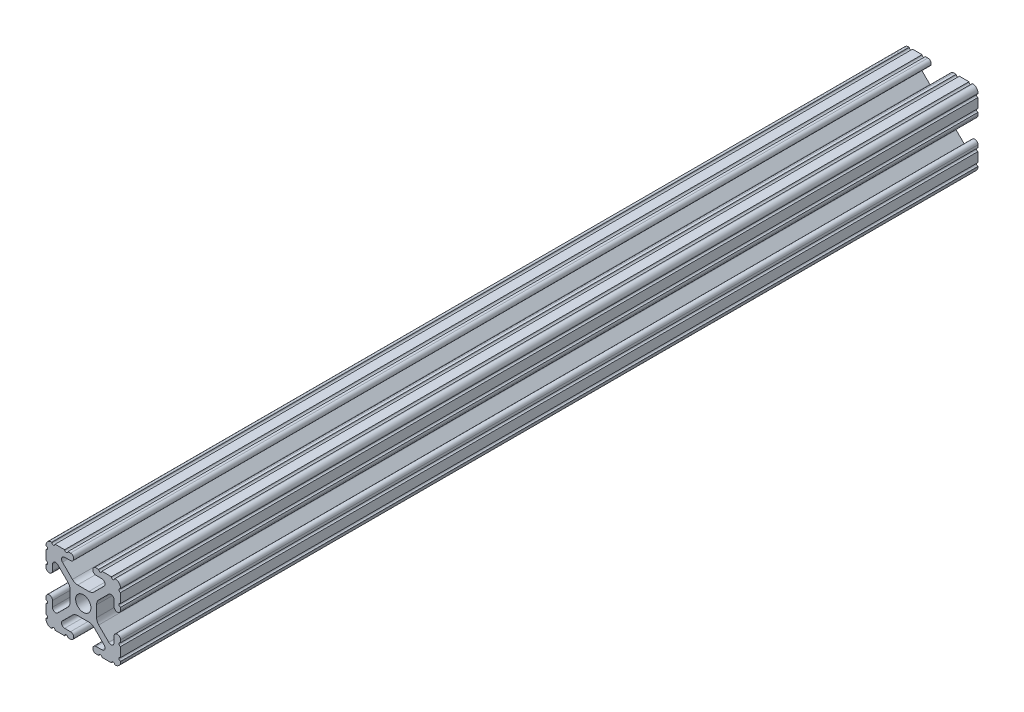
SolidWorks part; units mm, degrees
ref_plane "Front Plane" through (0, 0, 0) normal (0, 0, 1) x (1, 0, 0)
ref_plane "Top Plane" through (0, 0, 0) normal (0, 1, 0) x (1, 0, 0)
ref_plane "Right Plane" through (0, 0, 0) normal (1, 0, 0) x (0, 0, -1)
sketch "Sketch1" plane through (0, 0, 0) normal (0, 0, 1) x (1, 0, 0)
  line L0 (0, -12.7) -> (0, 12.7) construction
  line L1 (12.7, 0) -> (-12.7, 0) construction
  line L2 (3.2512, 12.7) -> (-3.2512, 12.7) construction
  line L3 (0, -4.5212) -> (0, 4.5212) construction
  line L4 (-3.2512, 12.7) -> (-3.2512, 10.4902) construction
  line L5 (12.7, -7.4168) -> (12.7, 7.4168) construction
  line L6 (0, -2.6035) -> (0, 2.6035) construction
  point P4 (0, 0)
  point P8 (0, 0)
  point P11 (0, 12.7)
  point P14 (0, 0)
  point P18 (12.7, 0)
  point P21 (0, 0)
sketch "Sketch2" plane through (0, 0, 0) normal (1, 0, 0) x (0, 0, -1)
  line L0 (-146.05, 0) -> (146.05, 0) construction
  point P4 (0, 0)
  dimension "Length" = 292.1
sketch "Sketch3" plane through (0, 0, 0) normal (0, 0, 1) x (1, 0, 0)
  line L1 (12.7, -12.7) -> (-12.7, -12.7)
  line L2 (12.7, -12.7) -> (12.7, 12.7)
  line L3 (12.7, 12.7) -> (-12.7, 12.7)
  line L4 (-12.7, -12.7) -> (-12.7, 12.7)
  line L5 (12.7, -12.7) -> (-12.7, 12.7) construction
  line L6 (12.7, 12.7) -> (-12.7, -12.7) construction
  point P0 (0, 0)
extrude "Boss-Extrude1" add sketch "Sketch3" along normal up to vertex (146.05 mm away) and the other way up to vertex (146.05 mm away) up to point (0, 0, 146.05) other way up to point (0, 0, -146.05)
sketch "Sketch4" plane through (0, 0, 146.05) normal (0, 0, 1) x (1, 0, 0)
  line L0 (-3.2512, 12.7) -> (-3.2512, 10.4902)
  line L1 (-3.2512, 10.4902) -> (-8.9276, 10.4902)
  line L2 (-8.9276, 10.4902) -> (-2.9586, 4.5212)
  line L3 (-2.9586, 4.5212) -> (2.9586, 4.5212)
  line L4 (0, -12.7) -> (0, 12.7) construction
  line L5 (12.7, 12.7) -> (-12.7, 12.7) construction
  line L6 (0, 12.7) -> (0, -12.7) construction
  line L7 (-12.7, 0) -> (12.7, 0) construction
  line L8 (-12.7, 12.7) -> (0, 0) construction
  line L9 (-12.7, 3.2512) -> (-10.4902, 3.2512)
  line L10 (-10.4902, 3.2512) -> (-10.4902, 8.9276)
  line L11 (-10.4902, 8.9276) -> (-4.5212, 2.9586)
  line L12 (-4.5212, 2.9586) -> (-4.5212, -2.9586)
  line L13 (4.5212, 2.9586) -> (4.5212, -2.9586)
  line L14 (10.4902, 8.9276) -> (4.5212, 2.9586)
  line L15 (10.4902, 3.2512) -> (10.4902, 8.9276)
  line L16 (12.7, 3.2512) -> (10.4902, 3.2512)
  line L17 (8.9276, 10.4902) -> (2.9586, 4.5212)
  line L18 (3.2512, 10.4902) -> (8.9276, 10.4902)
  line L19 (3.2512, 12.7) -> (3.2512, 10.4902)
  line L20 (3.2512, -12.7) -> (3.2512, -10.4902)
  line L21 (3.2512, -10.4902) -> (8.9276, -10.4902)
  line L22 (8.9276, -10.4902) -> (2.9586, -4.5212)
  line L23 (12.7, -3.2512) -> (10.4902, -3.2512)
  line L24 (10.4902, -3.2512) -> (10.4902, -8.9276)
  line L25 (10.4902, -8.9276) -> (4.5212, -2.9586)
  line L26 (-10.4902, -8.9276) -> (-4.5212, -2.9586)
  line L27 (-10.4902, -3.2512) -> (-10.4902, -8.9276)
  line L28 (-12.7, -3.2512) -> (-10.4902, -3.2512)
  line L29 (-2.9586, -4.5212) -> (2.9586, -4.5212)
  line L30 (-8.9276, -10.4902) -> (-2.9586, -4.5212)
  line L31 (-3.2512, -10.4902) -> (-8.9276, -10.4902)
  line L32 (-3.2512, -12.7) -> (-3.2512, -10.4902)
  line L33 (-12.7, 3.2512) -> (-12.7, -3.2512)
  line L34 (-3.2512, -12.7) -> (3.2512, -12.7)
  line L35 (12.7, -3.2512) -> (12.7, 3.2512)
  line L36 (3.2512, 12.7) -> (-3.2512, 12.7)
  line L37 (-12.7, 12.7) -> (-12.7, -12.7) construction
  line L38 (-12.7, -12.7) -> (12.7, -12.7) construction
  arc A3 (-6.3485, 10.4902) -> (-7.1039, 8.6665) centre (-6.3485, 9.4219) ccw
  arc A4 (7.1039, 8.6665) -> (6.3485, 10.4902) centre (6.3485, 9.4219) ccw
  arc A5 (8.6665, -7.1039) -> (10.4902, -6.3485) centre (9.4219, -6.3485) ccw
  arc A6 (10.4902, 6.3485) -> (8.6665, 7.1039) centre (9.4219, 6.3485) ccw
  arc A7 (-7.1039, -8.6665) -> (-6.3485, -10.4902) centre (-6.3485, -9.4219) ccw
  arc A8 (6.3485, -10.4902) -> (7.1039, -8.6665) centre (6.3485, -9.4219) ccw
  arc A9 (-8.6665, 7.1039) -> (-10.4902, 6.3485) centre (-9.4219, 6.3485) ccw
  arc A10 (-10.4902, -6.3485) -> (-8.6665, -7.1039) centre (-9.4219, -6.3485) ccw
  circle A11 centre (0, 0) radius 2.6035
  point P34 (0, 4.5212)
  point P45 (4.5212, 0)
  point P46 (-4.5212, 0)
  point P53 (0, -4.5212)
  point P81 (0, 0)
  line M2 (-12.7, 12.7) -> (-12.7, -12.7)
  line M3 (-12.7, -12.7) -> (12.7, -12.7)
  line M4 (12.7, -12.7) -> (12.7, 12.7)
  line M5 (12.7, 12.7) -> (-12.7, 12.7)
  dimension "D5" = 5.207
  dimension "D1" = 2.2098
  dimension "D2" = 2.2098
  dimension "D3" = 14.8336
  dimension "D4" = 4
extrude "Cut-Extrude1" cut sketch "Sketch4" against normal through all contours L17 A4 L18 L19 L0 L1 A3 L2 L3 M5 | L15 A6 L14 L13 L25 A5 L24 L23 L16 M4 | L21 A8 L22 L29 L30 A7 L31 L32 L20 M3 | L27 A10 L26 L12 L11 A9 L10 L9 L28 M2 | A11
sketch "Sketch5" plane through (0, 0, 146.05) normal (0, 0, 1) x (1, 0, 0)
  line L0 (-4.3561, 12.7) -> (-3.2512, 12.7)
  line L1 (-3.2512, 12.7) -> (-3.2512, 10.4902)
  line L2 (-3.2512, 10.4902) -> (-4.3561, 10.4902)
  line L3 (0, -12.7) -> (0, 12.7) construction
  line L4 (-3.2512, 12.7) -> (-12.7, 12.7) construction
  line L5 (3.2512, 10.4902) -> (4.3561, 10.4902)
  line L6 (3.2512, 12.7) -> (3.2512, 10.4902)
  line L7 (4.3561, 12.7) -> (3.2512, 12.7)
  line L8 (12.7, 4.3561) -> (12.7, 3.2512)
  line L9 (12.7, 3.2512) -> (10.4902, 3.2512)
  line L10 (10.4902, 3.2512) -> (10.4902, 4.3561)
  line L11 (10.4902, -3.2512) -> (10.4902, -4.3561)
  line L12 (12.7, -3.2512) -> (10.4902, -3.2512)
  line L13 (12.7, -4.3561) -> (12.7, -3.2512)
  line L14 (4.3561, -12.7) -> (3.2512, -12.7)
  line L15 (3.2512, -12.7) -> (3.2512, -10.4902)
  line L16 (3.2512, -10.4902) -> (4.3561, -10.4902)
  line L17 (-3.2512, -10.4902) -> (-4.3561, -10.4902)
  line L18 (-3.2512, -12.7) -> (-3.2512, -10.4902)
  line L19 (-4.3561, -12.7) -> (-3.2512, -12.7)
  line L20 (-12.7, -4.3561) -> (-12.7, -3.2512)
  line L21 (-12.7, -3.2512) -> (-10.4902, -3.2512)
  line L22 (-10.4902, -3.2512) -> (-10.4902, -4.3561)
  line L23 (-10.4902, 3.2512) -> (-10.4902, 4.3561)
  line L24 (-12.7, 3.2512) -> (-10.4902, 3.2512)
  line L25 (-12.7, 4.3561) -> (-12.7, 3.2512)
  line L26 (-12.7, 12.7) -> (-12.7, 3.2512) construction
  line L27 (-10.7124, 12.7) -> (-9.6075, 12.7)
  line L28 (-6.3436, 12.7) -> (-5.2387, 12.7)
  line L29 (-12.7, 10.7124) -> (-12.7, 9.6075)
  line L30 (-12.7, 6.3436) -> (-12.7, 5.2387)
  line L31 (6.3437, 12.7) -> (5.2388, 12.7)
  line L32 (10.7125, 12.7) -> (9.6076, 12.7)
  line L33 (12.7, 10.7125) -> (12.7, 9.6075)
  line L34 (12.7, 6.3436) -> (12.7, 5.2387)
  line L35 (12.7, -6.3437) -> (12.7, -5.2388)
  line L36 (12.7, -10.7125) -> (12.7, -9.6076)
  line L37 (10.7125, -12.7) -> (9.6076, -12.7)
  line L38 (6.3437, -12.7) -> (5.2388, -12.7)
  line L39 (-6.3436, -12.7) -> (-5.2387, -12.7)
  line L40 (-10.7124, -12.7) -> (-9.6075, -12.7)
  line L41 (-12.7, -10.7125) -> (-12.7, -9.6076)
  line L42 (-12.7, -6.3437) -> (-12.7, -5.2388)
  line L43 (12.7, 12.7) -> (3.2512, 12.7) construction
  line L44 (12.7, 3.2512) -> (12.7, 12.7) construction
  arc A0 (-4.3561, 10.4902) -> (-4.3561, 12.7) centre (-4.3561, 11.5951) ccw
  arc A1 (4.3561, 10.4902) -> (4.3561, 12.7) centre (4.3561, 11.5951) cw
  arc A2 (10.4902, 4.3561) -> (12.7, 4.3561) centre (11.5951, 4.3561) ccw
  arc A3 (10.4902, -4.3561) -> (12.7, -4.3561) centre (11.5951, -4.3561) cw
  arc A4 (4.3561, -10.4902) -> (4.3561, -12.7) centre (4.3561, -11.5951) ccw
  arc A5 (-4.3561, -10.4902) -> (-4.3561, -12.7) centre (-4.3561, -11.5951) cw
  arc A6 (-10.4902, -4.3561) -> (-12.7, -4.3561) centre (-11.5951, -4.3561) ccw
  arc A7 (-10.4902, 4.3561) -> (-12.7, 4.3561) centre (-11.5951, 4.3561) cw
  arc A8 (-10.7124, 12.7) -> (-9.6075, 12.7) centre (-10.16, 12.7) ccw
  arc A9 (-6.3436, 12.7) -> (-5.2387, 12.7) centre (-5.7912, 12.7) ccw
  arc A10 (-12.7, 9.6075) -> (-12.7, 10.7124) centre (-12.7, 10.16) ccw
  arc A11 (-12.7, 5.2387) -> (-12.7, 6.3436) centre (-12.7, 5.7912) ccw
  arc A12 (5.2388, 12.7) -> (6.3437, 12.7) centre (5.7912, 12.7) ccw
  arc A13 (9.6076, 12.7) -> (10.7125, 12.7) centre (10.16, 12.7) ccw
  arc A14 (12.7, 10.7125) -> (12.7, 9.6075) centre (12.7, 10.16) ccw
  arc A15 (12.7, 6.3436) -> (12.7, 5.2387) centre (12.7, 5.7912) ccw
  arc A16 (12.7, -5.2388) -> (12.7, -6.3437) centre (12.7, -5.7912) ccw
  arc A17 (12.7, -9.6076) -> (12.7, -10.7125) centre (12.7, -10.16) ccw
  arc A18 (10.7125, -12.7) -> (9.6076, -12.7) centre (10.16, -12.7) ccw
  arc A19 (6.3437, -12.7) -> (5.2388, -12.7) centre (5.7912, -12.7) ccw
  arc A20 (-5.2387, -12.7) -> (-6.3436, -12.7) centre (-5.7912, -12.7) ccw
  arc A21 (-9.6075, -12.7) -> (-10.7124, -12.7) centre (-10.16, -12.7) ccw
  arc A22 (-12.7, -10.7125) -> (-12.7, -9.6076) centre (-12.7, -10.16) ccw
  arc A23 (-12.7, -6.3437) -> (-12.7, -5.2388) centre (-12.7, -5.7912) ccw
  point P11 (0, 0)
  point P52 (0, 0)
  point P104 (0, 0)
  line M5 (3.2512, -10.4902) -> (3.2512, -12.7)
  line M6 (3.2512, -12.7) -> (12.7, -12.7)
  line M7 (12.7, -12.7) -> (12.7, -3.2512)
  line M8 (12.7, -3.2512) -> (10.4902, -3.2512)
  line M9 (10.4902, -3.2512) -> (10.4902, -6.3485)
  line M15 (10.4902, 6.3485) -> (10.4902, 3.2512)
  line M16 (10.4902, 3.2512) -> (12.7, 3.2512)
  line M17 (12.7, 3.2512) -> (12.7, 12.7)
  line M18 (12.7, 12.7) -> (3.2512, 12.7)
  line M19 (3.2512, 12.7) -> (3.2512, 10.4902)
  line M20 (3.2512, 10.4902) -> (6.3485, 10.4902)
  line M26 (-6.3485, 10.4902) -> (-3.2512, 10.4902)
  line M27 (-3.2512, 10.4902) -> (-3.2512, 12.7)
  line M28 (-3.2512, 12.7) -> (-12.7, 12.7)
  line M29 (-12.7, 12.7) -> (-12.7, 3.2512)
  line M30 (-12.7, 3.2512) -> (-10.4902, 3.2512)
  line M31 (-10.4902, 3.2512) -> (-10.4902, 6.3485)
  line M37 (-10.4902, -6.3485) -> (-10.4902, -3.2512)
  line M38 (-10.4902, -3.2512) -> (-12.7, -3.2512)
  line M39 (-12.7, -3.2512) -> (-12.7, -12.7)
  line M40 (-12.7, -12.7) -> (-3.2512, -12.7)
  line M41 (-3.2512, -12.7) -> (-3.2512, -10.4902)
  line M42 (-3.2512, -10.4902) -> (-6.3485, -10.4902)
  line M48 (6.3485, -10.4902) -> (3.2512, -10.4902)
  dimension "D2" = 0.5524
  dimension "D3" = 2.54
  dimension "D4" = 2.54
  dimension "D5" = 2.54
  dimension "D6" = 2.54
  dimension "D1" = 4
  dimension "D7" = 4
extrude "Cut-Extrude2" cut sketch "Sketch5" against normal through all contours A7 M30 M29 | A7 L24 M31 | A6 L21 M39 | A6 M37 M38 | A5 L18 M42 | A5 M41 M40 | A4 M48 M5 | A4 L15 M6 | A3 L12 M9 | A3 M8 M7 | A2 M15 M16 | A2 L9 M17 | A1 M19 M18 | A1 L6 M20 | A0 L1 M28 | A0 M26 M27 | A11 L30 | A10 L29 | A8 L27 | A9 L28 | L31 A12 | L32 A13 | L33 A14 | L34 A15 | L42 A23 | L41 A22 | L40 A21 | L39 A20 | L36 A17 | L35 A16 | L37 A18 | L38 A19
fillet "Fillet1" radius 2.54 8 edges at (2.9586, -4.5212, 0) (-2.9586, -4.5212, 0) (4.5212, -2.9586, 0) (4.5212, 2.9586, 0) (-2.9586, 4.5212, 0) (2.9586, 4.5212, 0) (-4.5212, -2.9586, 0) (-4.5212, 2.9586, 0)
fillet "Fillet2" radius 1.778 4 edges at (12.7, -12.7, 0) (12.7, 12.7, 0) (-12.7, -12.7, 0) (-12.7, 12.7, 0)
equation "\"D2@Sketch4\"=\"Thickness@Sketch1\""
equation "\"D1@Sketch4\"=\"Thickness@Sketch1\""
equation "\"D3@Sketch4\"=\"Opening Width@Sketch1\""
equation "\"D5@Sketch4\"=\"Hole Dia@Sketch1\""
equation "\"D2@Sketch5\"=\"Thickness@Sketch1\"/4"
equation "\"D3@Sketch5\"=\"Height@Sketch1\"/10"
equation "\"D4@Sketch5\"=\"D3@Sketch5\""
equation "\"D5@Sketch5\"=\"D4@Sketch5\""
equation "\"D6@Sketch5\"=\"D5@Sketch5\""
